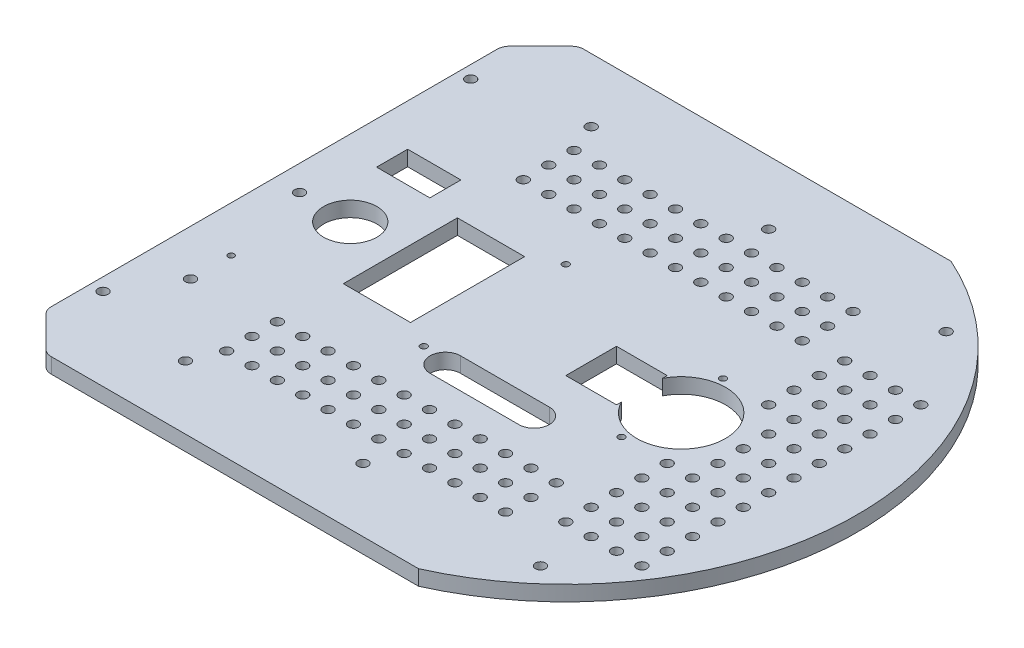
SolidWorks part; units mm, degrees
ref_plane "Front Plane" through (0, 0, 0) normal (0, 0, 1) x (1, 0, 0)
ref_plane "Top Plane" through (0, 0, 0) normal (0, 1, 0) x (1, 0, 0)
ref_plane "Right Plane" through (0, 0, 0) normal (1, 0, 0) x (0, 0, -1)
sketch "Sketch1" plane through (0, 0, 0) normal (0, 1, 0) x (1, 0, 0)
  line L0 (0, 80) -> (0, -80) construction
  line L1 (-46.9042, -105) -> (46.9042, -105)
  line L2 (-46.9042, 105) -> (46.9042, 105)
  line L7 (-70, 0) -> (70, 0) construction
  line L8 (-70, 80) -> (70, 80) construction
  line L9 (-70, 80) -> (-70, -80) construction
  line L10 (-70, -80) -> (70, -80) construction
  line L11 (70, 80) -> (70, -80) construction
  circle A0 centre (-70, 80) radius 2
  circle A1 centre (70, 80) radius 2
  circle A2 centre (70, -80) radius 2
  circle A3 centre (-70, -80) radius 2
  circle A4 centre (0, 80) radius 2
  circle A5 centre (70, 0) radius 2
  circle A6 centre (0, -80) radius 2
  arc A8 (-46.9042, 105) -> (-46.9042, -105) centre (0, 0) ccw
  arc A9 (46.9042, -105) -> (46.9042, 105) centre (0, 0) ccw
  point P0 (0, 0)
  point P13 (0, 0)
  dimension "D1" = 105
  dimension "D8" = 230
  dimension "D5" = 4
  dimension "D2" = 140
  dimension "D3" = 160
  dimension "D4" = 105
extrude "Boss-Extrude1" add sketch "Sketch1" along normal blind 6
sketch "Sketch2" plane through (0, 6, 0) normal (0, 1, 0) x (1, 0, 0)
  line L0 (0, 105) -> (0, -105) construction
  line L1 (46.9042, 105) -> (-46.9042, 105) construction
  line L2 (-46.9042, -105) -> (46.9042, -105) construction
  line L3 (-115, 0) -> (115, 0) construction
  line L4 (-17.5, -30) -> (17.5, -30) construction
  line L5 (-65.25, -22.5) -> (-38.75, -22.5)
  line L6 (-65.25, -22.5) -> (-65.25, 22.5)
  line L7 (-65.25, 22.5) -> (-38.75, 22.5)
  line L8 (-38.75, -22.5) -> (-38.75, 22.5)
  line L9 (-65.25, -22.5) -> (-38.75, 22.5) construction
  line L10 (-65.25, 22.5) -> (-38.75, -22.5) construction
  line L11 (-17.5, -24) -> (17.5, -24)
  line L12 (-17.5, -36) -> (17.5, -36)
  arc A0 (-46.9042, 105) -> (-46.9042, -105) centre (0, 0) ccw construction
  arc A1 (46.9042, -105) -> (46.9042, 105) centre (0, 0) ccw construction
  circle A2 centre (0, 0) radius 35 construction
  circle A3 centre (-28, 28) radius 1.3
  circle A4 centre (-28, -28) radius 1.3
  circle A5 centre (42, 20) radius 1.3
  circle A6 centre (42, -20) radius 1.3
  circle A7 centre (-85, 0) radius 10.5
  circle A8 centre (-97, -35) radius 1.2
  circle A10 centre (-97, -51) radius 2
  circle A12 centre (-105, 0) radius 2
  circle A13 centre (60, 50) radius 2
  circle A14 centre (70, 50) radius 2
  circle A15 centre (80, 50) radius 2
  circle A16 centre (90, 50) radius 2
  circle A17 centre (70, 40) radius 2
  circle A18 centre (80, 40) radius 2
  circle A19 centre (90, 40) radius 2
  circle A20 centre (70, 30) radius 2
  circle A21 centre (80, 30) radius 2
  circle A22 centre (90, 30) radius 2
  circle A23 centre (70, 20) radius 2
  circle A24 centre (80, 20) radius 2
  circle A25 centre (90, 20) radius 2
  circle A26 centre (70, 10) radius 2
  circle A27 centre (80, 10) radius 2
  circle A28 centre (90, 10) radius 2
  circle A29 centre (70, 0) radius 2
  circle A30 centre (80, 0) radius 2
  circle A31 centre (90, 0) radius 2
  circle A32 centre (70, -10) radius 2
  circle A33 centre (80, -10) radius 2
  circle A34 centre (90, -10) radius 2
  circle A35 centre (70, -20) radius 2
  circle A36 centre (80, -20) radius 2
  circle A37 centre (90, -20) radius 2
  circle A38 centre (70, -30) radius 2
  circle A39 centre (80, -30) radius 2
  circle A40 centre (90, -30) radius 2
  circle A41 centre (70, -40) radius 2
  circle A42 centre (80, -40) radius 2
  circle A43 centre (90, -40) radius 2
  circle A44 centre (70, -50) radius 2
  circle A45 centre (80, -50) radius 2
  circle A46 centre (90, -50) radius 2
  circle A47 centre (70, -60) radius 2
  circle A48 centre (80, -60) radius 2
  circle A49 centre (90, -60) radius 2
  circle A50 centre (60, 40) radius 2
  circle A51 centre (60, 30) radius 2
  circle A52 centre (60, 20) radius 2
  circle A56 centre (60, -20) radius 2
  circle A57 centre (60, -30) radius 2
  circle A58 centre (60, -40) radius 2
  circle A59 centre (60, -50) radius 2
  circle A60 centre (60, -60) radius 2
  arc A61 (-17.5, -24) -> (-17.5, -36) centre (-17.5, -30) ccw
  arc A62 (17.5, -36) -> (17.5, -24) centre (17.5, -30) ccw
  circle A63 centre (-65.25, -68.5) radius 2
  circle A64 centre (34.75, 48.5) radius 2
  circle A65 centre (-55.25, -68.5) radius 2
  circle A66 centre (-45.25, -68.5) radius 2
  circle A67 centre (-35.25, -68.5) radius 2
  circle A68 centre (-25.25, -68.5) radius 2
  circle A69 centre (-15.25, -68.5) radius 2
  circle A70 centre (-5.25, -68.5) radius 2
  circle A71 centre (4.75, -68.5) radius 2
  circle A72 centre (14.75, -68.5) radius 2
  circle A73 centre (24.75, -68.5) radius 2
  circle A74 centre (34.75, -68.5) radius 2
  circle A75 centre (44.75, -68.5) radius 2
  circle A76 centre (-55.25, -58.5) radius 2
  circle A77 centre (-45.25, -58.5) radius 2
  circle A78 centre (-35.25, -58.5) radius 2
  circle A79 centre (-25.25, -58.5) radius 2
  circle A80 centre (-15.25, -58.5) radius 2
  circle A81 centre (-5.25, -58.5) radius 2
  circle A82 centre (4.75, -58.5) radius 2
  circle A83 centre (14.75, -58.5) radius 2
  circle A84 centre (24.75, -58.5) radius 2
  circle A85 centre (34.75, -58.5) radius 2
  circle A86 centre (44.75, -58.5) radius 2
  circle A87 centre (-55.25, -48.5) radius 2
  circle A88 centre (-45.25, -48.5) radius 2
  circle A89 centre (-35.25, -48.5) radius 2
  circle A90 centre (-25.25, -48.5) radius 2
  circle A91 centre (-15.25, -48.5) radius 2
  circle A92 centre (-5.25, -48.5) radius 2
  circle A93 centre (4.75, -48.5) radius 2
  circle A94 centre (14.75, -48.5) radius 2
  circle A95 centre (24.75, -48.5) radius 2
  circle A96 centre (34.75, -48.5) radius 2
  circle A97 centre (44.75, -48.5) radius 2
  circle A98 centre (-65.25, -58.5) radius 2
  circle A99 centre (-65.25, -48.5) radius 2
  circle A100 centre (44.75, 48.5) radius 2
  circle A101 centre (44.75, 58.5) radius 2
  circle A102 centre (34.75, 58.5) radius 2
  circle A103 centre (34.75, 68.5) radius 2
  circle A104 centre (44.75, 68.5) radius 2
  circle A105 centre (24.75, 48.5) radius 2
  circle A106 centre (24.75, 58.5) radius 2
  circle A107 centre (24.75, 68.5) radius 2
  circle A108 centre (14.75, 68.5) radius 2
  circle A109 centre (14.75, 58.5) radius 2
  circle A110 centre (14.75, 48.5) radius 2
  circle A111 centre (4.75, 48.5) radius 2
  circle A112 centre (4.75, 58.5) radius 2
  circle A113 centre (4.75, 68.5) radius 2
  circle A114 centre (-5.25, 68.5) radius 2
  circle A115 centre (-5.25, 58.5) radius 2
  circle A116 centre (-5.25, 48.5) radius 2
  circle A117 centre (-15.25, 48.5) radius 2
  circle A118 centre (-15.25, 58.5) radius 2
  circle A119 centre (-15.25, 68.5) radius 2
  circle A120 centre (-25.25, 68.5) radius 2
  circle A121 centre (-25.25, 58.5) radius 2
  circle A122 centre (-25.25, 48.5) radius 2
  circle A123 centre (-35.25, 48.5) radius 2
  circle A124 centre (-35.25, 68.5) radius 2
  circle A125 centre (-35.25, 58.5) radius 2
  circle A126 centre (-45.25, 68.5) radius 2
  circle A127 centre (-45.25, 58.5) radius 2
  circle A128 centre (-45.25, 48.5) radius 2
  circle A129 centre (-55.25, 48.5) radius 2
  circle A130 centre (-55.25, 58.5) radius 2
  circle A131 centre (-55.25, 68.5) radius 2
  circle A132 centre (-65.25, 68.5) radius 2
  circle A133 centre (-65.25, 48.5) radius 2
  circle A134 centre (-65.25, 58.5) radius 2
  circle A135 centre (45.5, 0) radius 17.5
  circle A136 centre (60, 0) radius 2 [skipped]
  circle A137 centre (60, 10) radius 2 [skipped]
  circle A138 centre (60, -10) radius 2 [skipped]
  point P28 (-52, 0)
  point P46 (0, -30)
  dimension "D1" = 70
  dimension "D2" = 2.6
  dimension "D9" = 21
  dimension "D14" = 2.4
  dimension "D20" = 4
  dimension "D21" = 4
  dimension "D24" = 4
  dimension "D29" = 6
  dimension "D31" = 35
  dimension "D32" = 4
  dimension "D3" = 28
  dimension "D4" = 42
  dimension "D5" = 40
  dimension "D6" = 56
  dimension "D7" = 28
  dimension "D8" = 20
  dimension "D10" = 85
  dimension "D11" = 26.5
  dimension "D12" = 45
  dimension "D13" = 52
  dimension "D16" = 35
  dimension "D17" = 18
  dimension "D18" = 16
  dimension "D22" = 10
  dimension "D23" = 50
  dimension "D25" = 60
  dimension "D28" = 35
  dimension "D30" = 30
  dimension "D33" = 46
  dimension "D34" = 45.5
  dimension "D26" = 4
  dimension "D27" = 12
  dimension "D35" = 12
  dimension "D36" = 3
extrude "Cut-Extrude1" cut sketch "Sketch2" against normal blind 10
ref_plane "Plane1" through (0, 6, 0) normal (0, 1, 0) x (1, 0, 0)
sketch "Sketch3" plane through (0, 6, 0) normal (0, 1, 0) x (1, 0, 0)
  line L0 (-46.9042, 105) -> (-115, 105)
  line L1 (-46.9042, -105) -> (-115, -105)
  line L2 (-115, -105) -> (-115, 105)
  arc A1 (-46.9042, 105) -> (-46.9042, -105) centre (0, 0) ccw construction
  arc A2 (-46.9042, 105) -> (-46.9042, -105) centre (0, 0) ccw
  dimension "D1" = 68.0958
extrude "Boss-Extrude2" add sketch "Sketch3" against normal blind 6 contours A2 L0 L2 | A2 L2 L1
chamfer "Chamfer1" distance 15 angle 45 2 edges at (-115, 3, -105) (-115, 3, 105)
fillet "Fillet1" radius 5 4 edges at (-100, 3, 105) (-115, 3, 90) (-115, 3, -90) (-100, 3, -105)
sketch "Sketch4" plane through (0, 6, 0) normal (0, 1, 0) x (1, 0, 0)
  line L0 (-115, 0) -> (110.0849, 0) construction
  line L1 (-115, -87.9289) -> (-115, 87.9289) construction
  circle A0 centre (-110, 72.5) radius 2
  circle A1 centre (-110, -72.5) radius 2
  dimension "D1" = 4
  dimension "D2" = 4
  dimension "D3" = 5
  dimension "D4" = 72.5
  dimension "D5" = 72.5
extrude "Cut-Extrude2" cut sketch "Sketch4" against normal blind 10
sketch "Sketch5" plane through (0, 6, 0) normal (0, 1, 0) x (1, 0, 0)
  line L0 (-115, -87.9289) -> (-115, 87.9289) construction
  line L1 (-98.5, 36.125) -> (-77.5, 36.125)
  line L2 (-98.5, 36.125) -> (-98.5, 23.875)
  line L3 (-98.5, 23.875) -> (-77.5, 23.875)
  line L4 (-77.5, 36.125) -> (-77.5, 23.875)
  line L5 (-98.5, 36.125) -> (-77.5, 23.875) construction
  line L6 (-98.5, 23.875) -> (-77.5, 36.125) construction
  line L7 (46.9042, 105) -> (-97.9289, 105) construction
  point P0 (-88, 30)
  dimension "D1" = 12.25
  dimension "D2" = 21
  dimension "D3" = 27
  dimension "D4" = 75
extrude "Cut-Extrude3" cut sketch "Sketch5" against normal blind 10
sketch "Sketch6" plane through (0, 6, 0) normal (0, 1, 0) x (1, 0, 0)
  line L0 (46.9042, 105) -> (-97.9289, 105) construction
  line L1 (30, 10) -> (10, 10)
  line L2 (30, 10) -> (30, -10)
  line L3 (30, -10) -> (10, -10)
  line L4 (10, 10) -> (10, -10)
  line L5 (30, 10) -> (10, -10) construction
  line L6 (30, -10) -> (10, 10) construction
  point P0 (20, 0)
  dimension "D1" = 20
  dimension "D2" = 20
  dimension "D3" = 20
  dimension "D4" = 105
extrude "Cut-Extrude4" cut sketch "Sketch6" against normal blind 10
